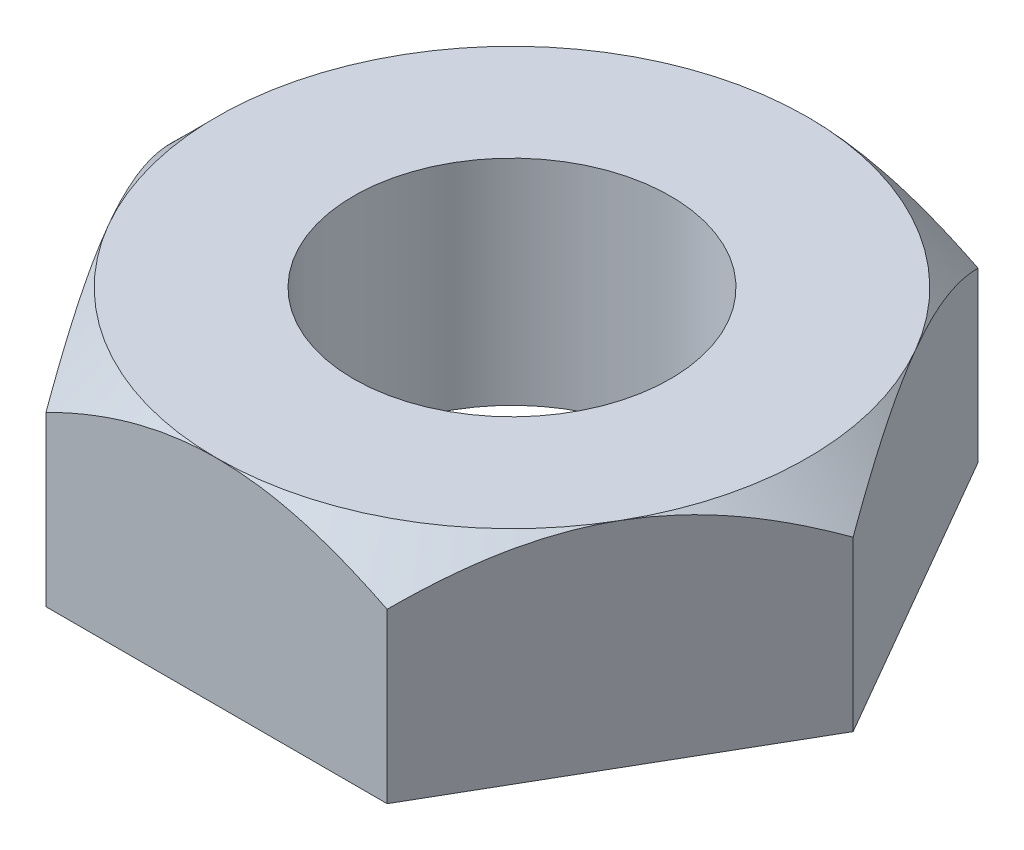
SolidWorks part; units mm, degrees
material "1060 Alloy"
ref_plane "Front Plane" through (0, 0, 0) normal (0, 0, 1) x (1, 0, 0)
ref_plane "Top Plane" through (0, 0, 0) normal (0, 1, 0) x (1, 0, 0)
ref_plane "Right Plane" through (0, 0, 0) normal (1, 0, 0) x (0, 0, -1)
sketch "Sketch1" plane through (0, 0, 0) normal (0, 1, 0) x (1, 0, 0)
  line L1 (39.8372, 0) -> (19.9186, 34.5)
  line L2 (19.9186, 34.5) -> (-19.9186, 34.5)
  line L3 (-19.9186, 34.5) -> (-39.8372, 0)
  line L4 (-39.8372, 0) -> (-19.9186, -34.5)
  line L5 (-19.9186, -34.5) -> (19.9186, -34.5)
  line L6 (19.9186, -34.5) -> (39.8372, 0)
  circle A0 centre (0, 0) radius 34.5 construction
  circle A1 centre (0, 0) radius 18.5
  dimension "D2" = 37
  dimension "D1" = 69
extrude "Boss-Extrude1" add sketch "Sketch1" along normal blind 25
sketch "Sketch2" plane through (0, 25, 0) normal (0, 1, 0) x (1, 0, 0)
  circle A0 centre (0, 0) radius 34.5
  dimension "D1" = 69
extrude "Cut-Extrude1" cut sketch "Sketch2" against normal mid plane 20 draft 45 flip side to cut
ref_plane "Plane1" through (0, 12.5, 0) normal (0, 1, 0) x (1, 0, 0)
